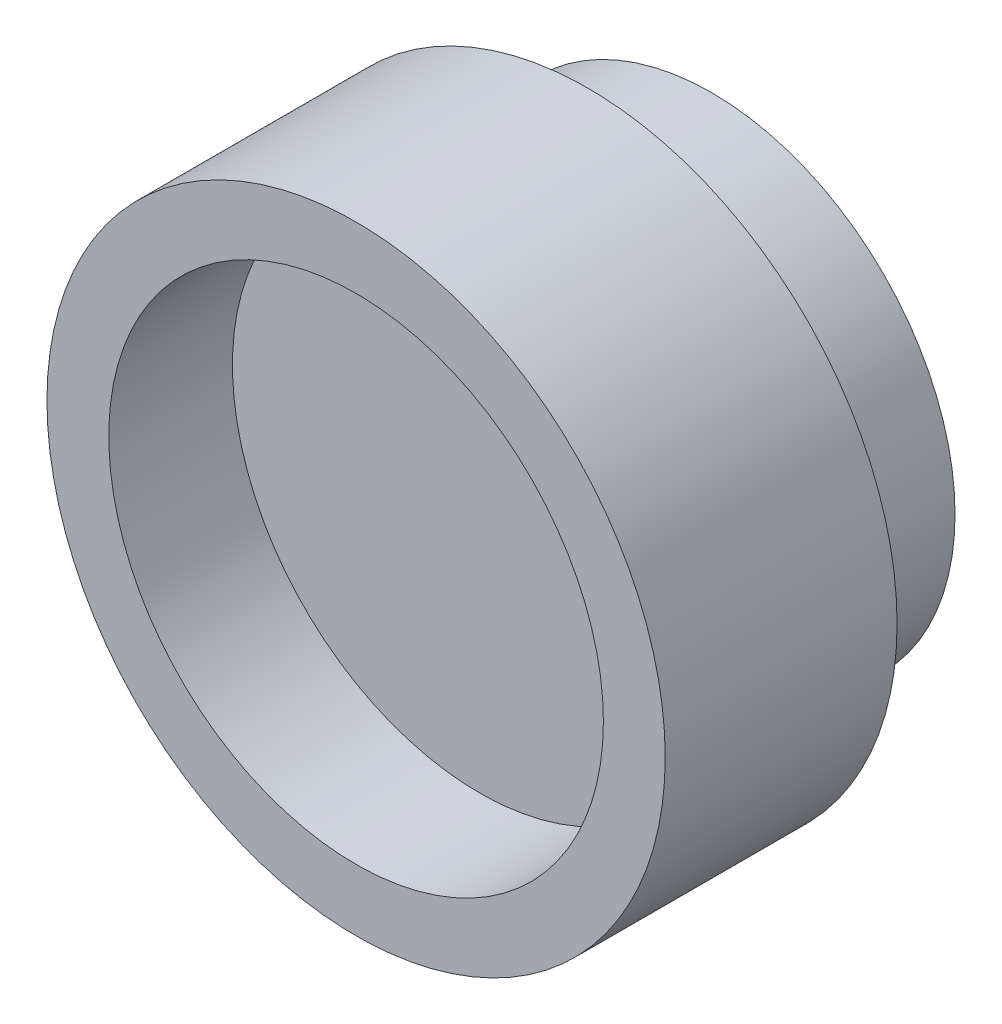
SolidWorks part; units mm, degrees
material "AISI 316 Annealed Stainless Steel Bar (SS)"
ref_plane "Front Plane" through (0, 0, 0) normal (0, 0, 1) x (1, 0, 0)
ref_plane "Top Plane" through (0, 0, 0) normal (0, 1, 0) x (1, 0, 0)
ref_plane "Right Plane" through (0, 0, 0) normal (1, 0, 0) x (0, 0, -1)
sketch "Sketch1" plane through (0, 0, 0) normal (0, 0, 1) x (1, 0, 0)
  circle A0 centre (0, 0) radius 15.75
  dimension "D1" = 31.5
extrude "Boss-Extrude1" add sketch "Sketch1" along normal blind 23
sketch "Sketch2" plane through (0, 0, 23) normal (0, 0, 1) x (1, 0, 0)
  circle A0 centre (0, 0) radius 20
  dimension "D1" = 40
extrude "Boss-Extrude2" add sketch "Sketch2" against normal offset from surface (15 mm away) 8 up to face at (15.75, 0, 0)
sketch "Sketch3" plane through (0, 0, 23) normal (0, 0, 1) x (1, 0, 0)
  circle A0 centre (0, 0) radius 16
  dimension "D1" = 32
extrude "Cut-Extrude1" cut sketch "Sketch3" against normal blind 8
